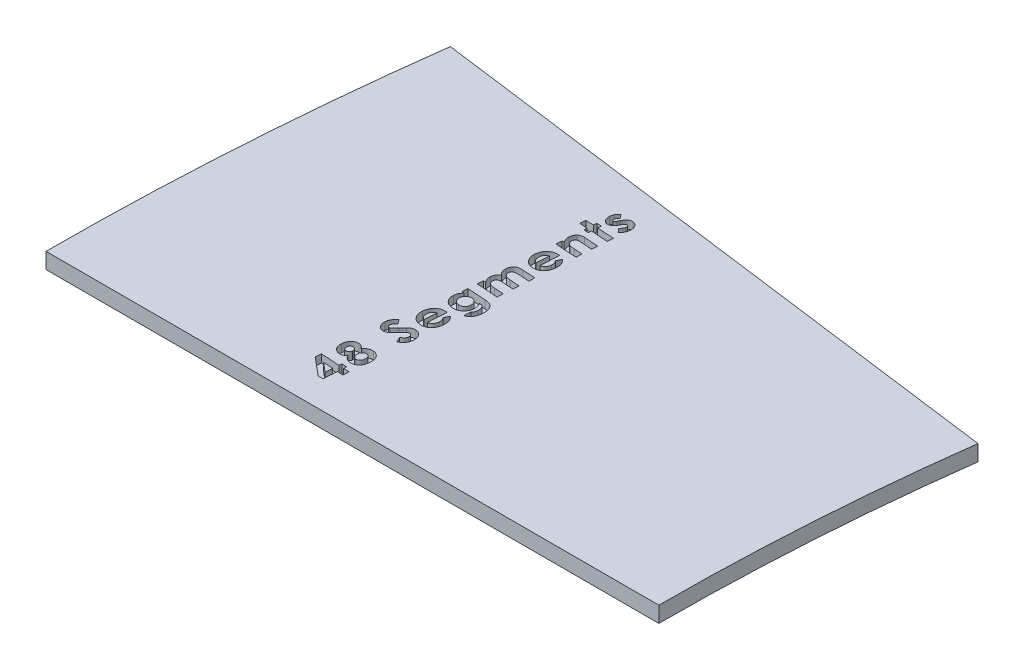
SolidWorks part; units mm, degrees
ref_plane "Front Plane" through (0, 0, 0) normal (0, 0, 1) x (1, 0, 0)
ref_plane "Top Plane" through (0, 0, 0) normal (0, 1, 0) x (1, 0, 0)
ref_plane "Right Plane" through (0, 0, 0) normal (1, 0, 0) x (0, 0, -1)
sketch "Sketch1" plane through (0, 0, 0) normal (0, 1, 0) x (1, 0, 0)
  line L0 (0, 0) -> (123.0584, 0)
  line L1 (127, 60.1377) -> (4.9944, 76.2)
  arc A0 (0, 0) -> (4.9944, 76.2) centre (583.7909, 0) cw
  arc A1 (123.0584, 0) -> (127, 60.1377) centre (583.7909, 0) cw
  dimension "D1" = 7.5
  dimension "D2" = 76.2
  dimension "D3" = 127
extrude "Boss-Extrude1" add sketch "Sketch1" along normal blind 3.175
sketch "Sketch2" plane through (0, 3.175, 0) normal (0, 1, 0) x (1, 0, 0)
  line L0 (50.8, 0) -> (55.3598, 69.5693) construction
  line L1 (0, 0) -> (123.0584, 0) construction
  line L2 (127, 60.1377) -> (4.9944, 76.2) construction
  text T0 "<b>48 Segments</b>" font "Century Gothic" height in points 22
  dimension "D1" = 50.8
  dimension "D2" = 50.8
extrude "Cut-Extrude1" cut sketch "Sketch2" against normal blind 1.5875
